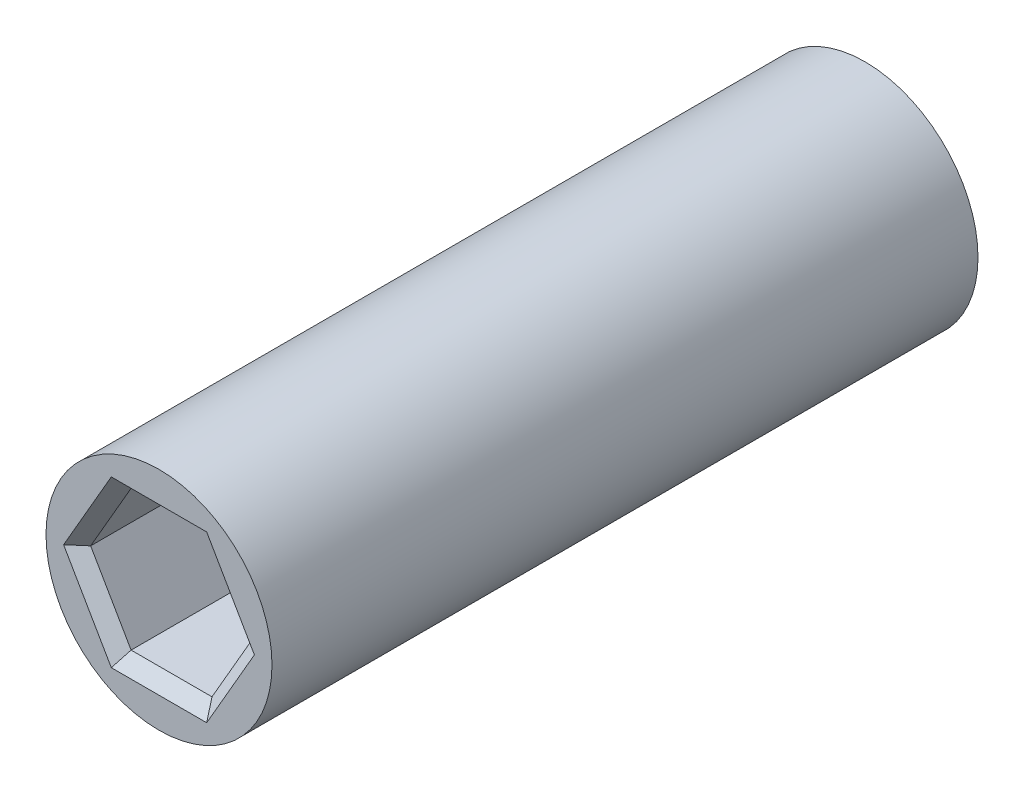
SolidWorks part; units mm, degrees
ref_plane "Front Plane" through (0, 0, 0) normal (0, 0, 1) x (1, 0, 0)
ref_plane "Top Plane" through (0, 0, 0) normal (0, 1, 0) x (1, 0, 0)
ref_plane "Right Plane" through (0, 0, 0) normal (1, 0, 0) x (0, 0, -1)
sketch "Sketch1" plane through (0, 0, 0) normal (0, 1, 0) x (1, 0, 0)
  line L0 (0, 0) -> (0, 63.1171) construction
  line L1 (0, 45.6171) -> (0, 17.5)
  point P3 (0, 39.1171)
  point P4 (0, 24)
  point P5 (0, 45.6171)
  point P6 (0, 17.5)
  dimension "D1" = 63.1171
  dimension "D2" = 24
  dimension "D3" = 24
  dimension "D4" = 15.1171
  dimension "D5" = 6.5
  dimension "D6" = 6.5
revolve "Revolve-Thin1" add sketch "Sketch1" angle 360 about L0 wall 4.5
sketch "Sketch2" plane through (0, 0, -17.5) normal (0, 0, 1) x (1, 0, 0)
  line L1 (1.6108, 2.79) -> (-1.6108, 2.79)
  line L2 (-1.6108, 2.79) -> (-3.2216, 0)
  line L3 (-3.2216, 0) -> (-1.6108, -2.79)
  line L4 (-1.6108, -2.79) -> (1.6108, -2.79)
  line L5 (1.6108, -2.79) -> (3.2216, 0)
  line L6 (3.2216, 0) -> (1.6108, 2.79)
  circle A0 centre (0, 0) radius 2.79 construction
  dimension "D1" = 5.58
extrude "Cut-Extrude1" cut sketch "Sketch2" against normal blind 7
sketch "Sketch3" plane through (0, 0, -45.6171) normal (0, 0, -1) x (-1, 0, 0)
  line L1 (1.6108, 2.79) -> (-1.6108, 2.79)
  line L2 (-1.6108, 2.79) -> (-3.2216, 0)
  line L3 (-3.2216, 0) -> (-1.6108, -2.79)
  line L4 (-1.6108, -2.79) -> (1.6108, -2.79)
  line L5 (1.6108, -2.79) -> (3.2216, 0)
  line L6 (3.2216, 0) -> (1.6108, 2.79)
  circle A0 centre (0, 0) radius 2.79 construction
  dimension "D1" = 5.58
extrude "Cut-Extrude2" cut sketch "Sketch3" against normal blind 7
chamfer "Chamfer1" distance 0.5 angle 45 12 edges at (2.4162, 1.395, -17.5) (2.4162, -1.395, -17.5) (0, -2.79, -17.5) (-2.4162, -1.395, -17.5) (-2.4162, 1.395, -17.5) (0, 2.79, -17.5) (0, 2.79, -45.6171) (-2.4162, 1.395, -45.6171) (-2.4162, -1.395, -45.6171) (0, -2.79, -45.6171) (2.4162, -1.395, -45.6171) (2.4162, 1.395, -45.6171)
